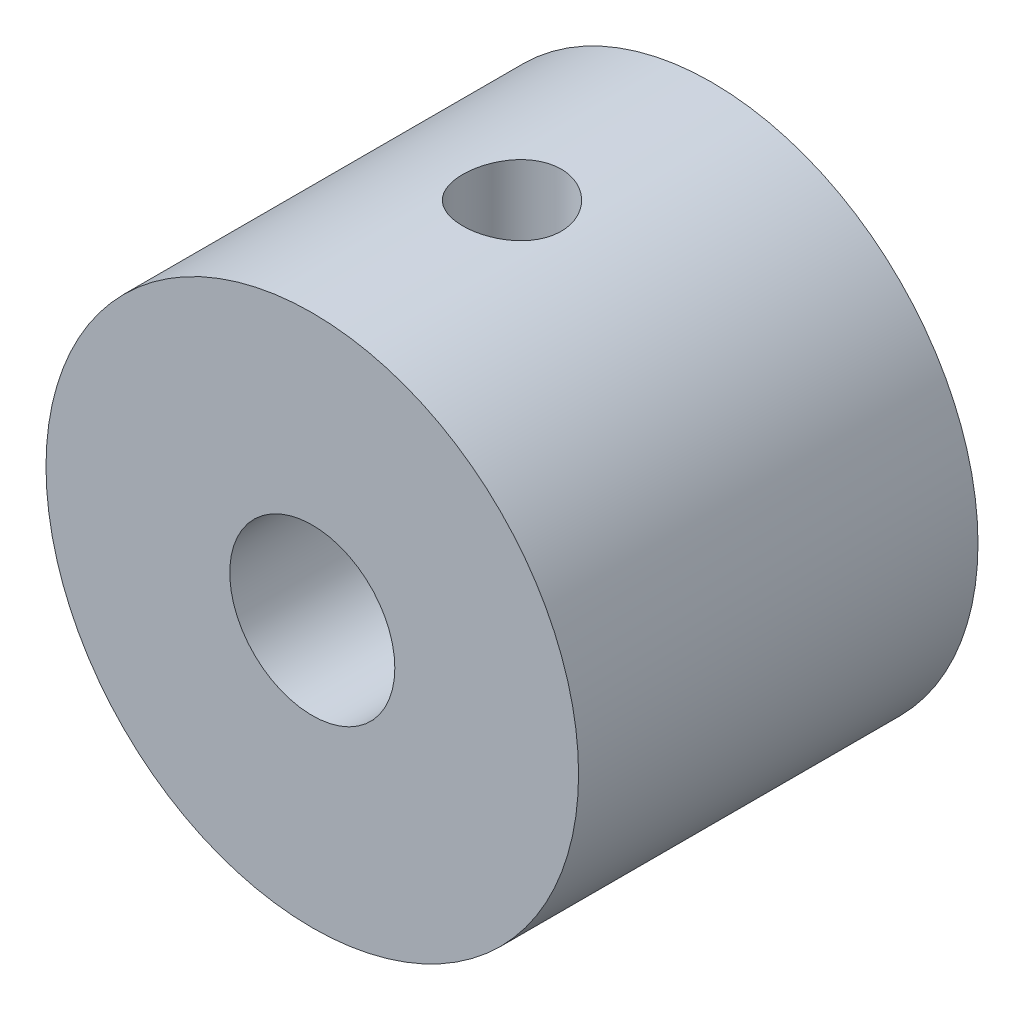
SolidWorks part; units mm, degrees
ref_plane "정면" through (0, 0, 0) normal (0, 0, 1) x (1, 0, 0)
ref_plane "윗면" through (0, 0, 0) normal (0, 1, 0) x (1, 0, 0)
ref_plane "우측면" through (0, 0, 0) normal (1, 0, 0) x (0, 0, -1)
sketch "스케치1" plane through (0, 0, 0) normal (0, 0, 1) x (1, 0, 0)
  circle A0 centre (0, 0) radius 3.1
  circle A1 centre (0, 0) radius 10
  dimension "D1" = 20
  dimension "D2" = 6.2
extrude "보스-돌출1" add sketch "스케치1" along normal blind 15
sketch "스케치2" plane through (0, 0, 0) normal (0, 1, 0) x (1, 0, 0)
  line L0 (-10, -7.5) -> (10, -7.5) construction
  line L3 (-10, 0) -> (-10, -15) construction
  line L4 (10, -15) -> (10, 0) construction
  circle A0 centre (0, -7.5) radius 1.85
  point P2 (0, 0)
  dimension "D1" = 3.7
extrude "컷-돌출1" cut sketch "스케치2" along normal through all contours A0
